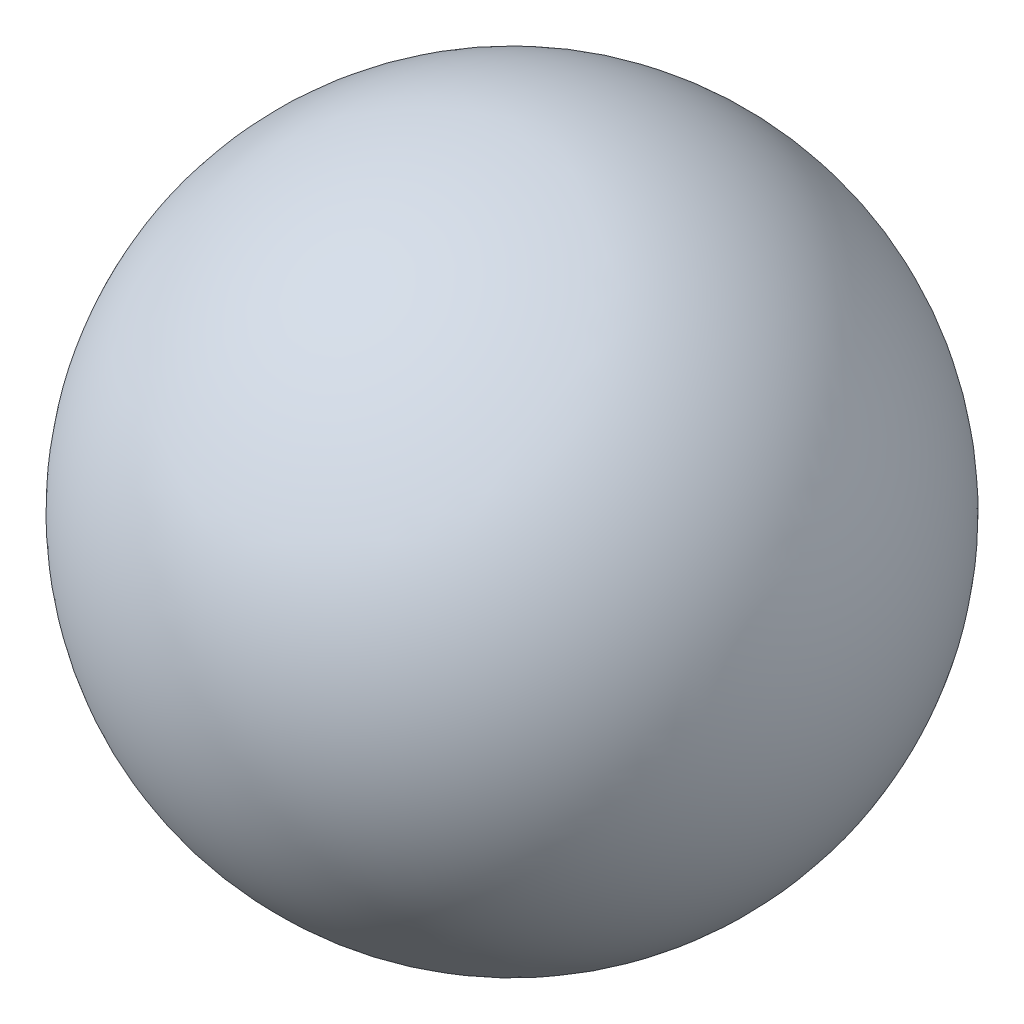
SolidWorks part; units mm, degrees
ref_plane "Plan de face" through (0, 0, 0) normal (0, 0, 1) x (1, 0, 0)
ref_plane "Plan de dessus" through (0, 0, 0) normal (0, 1, 0) x (1, 0, 0)
ref_plane "Plan de droite" through (0, 0, 0) normal (1, 0, 0) x (0, 0, -1)
sketch "Esquisse1" plane through (0, 0, 0) normal (0, 1, 0) x (1, 0, 0)
  line L0 (-250, 0) -> (250, 0)
  arc A0 (250, 0) -> (-250, 0) centre (0, 0) ccw
  dimension "D1" = 500
revolve "Révolution1" add sketch "Esquisse1" angle 360 about L0
ref_plane "Plan1" through (0, 0, 380) normal (0, 0, 1) x (1, 0, 0)
sketch "Esquisse2" plane through (0, 0, 380) normal (0, 0, 1) x (1, 0, 0)
  circle A0 centre (0, 0) radius 91.4874
curve "Hélice/Spirale1"
ref_plane "Plan2" through (0, 0, 350) normal (0, 0, 1) x (1, 0, 0)
sketch "Esquisse3" plane through (0, 0, 350) normal (0, 0, 1) x (1, 0, 0)
  spline S0 degree 3 poles (1010.474, 1620.8253) (291.317, -332.6838) (-108.2126, -145.3785) (-90.5411, 17.9971) (-89.7214, 22.4688) (-87.4254, 31.2681) (-85.9491, 35.5958) (-82.3643, 44.0105) (-80.2559, 48.0976) (-75.446, 55.9391) (-72.7445, 59.6934) (-66.8008, 66.7831) (-63.5586, 70.1186) (-56.5982, 76.2929) (-52.8801, 79.1317) (-45.044, 84.2449) (-40.9261, 86.5193) (-32.3759, 90.4475) (-27.9438, 92.1013) (-18.8588, 94.7452) (-14.206, 95.7352) (-4.779, 97.0226) (-0.0049, 97.3199) (9.5614, 97.2076) (14.3537, 96.7979) (23.8516, 95.2729) (28.5572, 94.1574) (37.7781, 91.2375) (42.2933, 89.433) (51.0323, 85.1669) (55.2561, 82.7053) (63.3169, 77.1718) (67.1537, 74.0999) (74.3525, 67.4063) (77.7143, 63.7847) (83.8843, 56.065) (86.6924, 51.967) (91.6877, 43.3792) (93.8748, 38.8894) (97.5737, 29.612) (99.0854, 24.8245) (101.3932, 15.0532) (102.1893, 10.0695) (103.041, 0.0128) (103.0965, -5.0601) (102.4582, -15.1853) (101.7643, -20.2374) (99.6345, -30.2103) (98.1985, -35.131) (94.6082, -44.7321) (92.4539, -49.4124) (87.4667, -58.4279) (84.6338, -62.763) (78.3443, -70.9897) (74.8878, -74.8813) (67.4203, -82.1315) (63.4094, -85.4901) (54.9152, -91.5953) (50.432, -94.342) (41.0863, -99.1572) (36.224, -101.2258) (26.2226, -104.633) (21.0836, -105.9715) (10.6385, -107.882) (5.3325, -108.4539) (-5.3325, -108.8111) (-10.6913, -108.5963) (-21.3453, -107.3771) (-26.6404, -106.3726) (-37.0505, -103.588) (-42.1654, -101.8079) (-52.1018, -97.5034) (-56.9232, -94.9791) (-66.1641, -89.2341) (-70.5837, -86.0134) (-78.9207, -78.9393) (-82.838, -75.0859) (-90.0801, -66.8244) (-93.4048, -62.4163) (-99.3834, -53.1365) (-102.0372, -48.2648) (-106.6095, -38.1595) (-108.528, -32.9261) (-111.5809, -22.2083) (-112.7153, -16.724) (-114.1676, -5.622) (-114.4856, -0.0042) (-114.2907, 11.2433) (-113.7778, 16.8731) (-111.9243, 28.0219) (-110.5838, 33.5408) (-107.0968, 44.3465) (-104.9504, 49.6332) (-99.8908, 59.8567) (-96.9777, 64.7935) (-90.4415, 74.2061) (-86.8184, 78.682) (-78.9346, 87.071) (-74.674, 90.984) (-65.6023, 98.1567) (-60.7914, 101.4163) (-50.7191, 107.205) (-45.4578, 109.7341) (-34.5956, 114.0001) (-28.9948, 115.7368) (-17.5726, 118.373) (-11.7514, 119.2724) (-0.0135, 120.2067) (5.9031, 120.2416) (17.7033, 119.4382) (23.5869, 118.6001) (35.1926, 116.0612) (40.9146, 114.3605) (52.0708, 110.1261) (57.5049, 107.5924) (67.9641, 101.7399) (72.9891, 98.421) (82.517, 91.0638) (87.0198, 87.0253) (95.4004, 78.3107) (99.2781, 73.6345) (106.3185, 63.7407) (109.4811, 58.5232) (115.016, 47.656) (117.3883, 42.0063) (121.2841, 30.3942) (122.8075, 24.4318) (124.965, 12.3217) (125.599, 6.1741) (125.9562, -6.1741) (125.6793, -12.3745) (124.2131, -24.6935) (123.0237, -30.8119) (119.7505, -42.8328) (117.6667, -48.7351) (112.6426, -60.1931) (109.7023, -65.7487) (103.0221, -76.3892) (99.2822, -81.474) (91.0777, -91.0582) (86.6132, -95.5574) (77.0505, -103.8674) (71.9525, -107.678) (61.2289, -114.5219) (55.6034, -117.5551) (43.9431, -122.7716) (37.9084, -124.9548) (25.5578, -128.4167) (19.2421, -129.6953) (6.4649, -131.3127) (0.0036, -131.6514) (-12.9252, -131.3738) (-19.3925, -130.7576) (-32.1921, -128.5758) (-38.5244, -127.0102) (-50.915, -122.9562) (-56.9731, -120.4677) (-68.6811, -114.6147) (-74.3308, -111.2501) (-85.0954, -103.7112) (-90.2103, -99.5369) (-99.7895, -90.4629) (-104.2537, -85.5632) (-112.4291, -75.1396) (-116.1402, -69.6157) (-122.7224, -58.059) (-125.5935, -52.0262) (-130.4264, -39.5792) (-132.3883, -33.165) (-135.3529, -20.092) (-136.3556, -13.4332) (-137.3724, -0.0142) (-137.3866, 6.746) (-136.4183, 20.2214) (-135.4358, 26.9365) (-132.488, 40.1749) (-130.5226, 46.6982) (-125.6441, 59.4095) (-122.7309, 65.5973) (-116.013, 77.5003) (-112.2083, 83.2153) (-103.7832, 94.0443) (-99.1629, 99.1583) (-89.201, 108.6692) (-83.8596, 113.0661) (-72.5663, 121.0417) (-66.6145, 124.6202) (-54.2256, 130.8748) (-47.7886, 133.5509) (-34.5658, 137.9352) (-27.78, 139.6435) (-14.005, 142.048) (-7.0157, 142.7441) (7.0157, 143.1013) (14.0577, 142.7623) (28.0417, 141.0491) (34.9835, 139.6748) (48.6151, 135.913) (55.3047, 133.5255) (68.2843, 127.7817) (74.5742, 124.4255) (86.6143, 116.8101) (92.3644, 112.5511) (103.1957, 103.2162) (108.2768, 98.1405) (117.6546, 87.2767) (121.9511, 81.4887) (129.6604, 69.3214) (133.073, 62.9421) (138.9336, 49.7267) (141.3816, 42.8907) (145.2524, 28.9074) (146.6753, 21.7602) (148.4577, 7.3079) (148.8171, 0.0029) (148.457, -14.607) (147.7374, -21.9119) (145.2272, -36.3624) (143.4366, -43.508) (138.8155, -57.4834) (135.985, -64.313) (129.3386, -77.5054) (125.5225, -83.8681) (116.9809, -95.9847) (112.2554, -101.7386) (101.9912, -112.508) (96.4525, -117.5234) (84.677, -126.7015) (78.4401, -130.864) (65.3989, -138.2397) (58.5946, -141.4528) (44.5628, -146.8528) (37.3353, -149.0397) (22.6114, -152.3327) (15.1151, -153.4387) (0.0148, -154.5381) (-7.589, -154.5316) (-22.7395, -153.3983) (-30.286, -152.2716) (-45.1572, -148.9148) (-52.4818, -146.6847) (-66.7482, -141.162) (-73.6898, -137.8694) (-87.0365, -130.2862) (-93.4414, -125.9955) (-105.5716, -116.5026) (-111.2968, -111.3004) (-121.9381, -100.0914) (-126.8542, -94.0846) (-135.7648, -81.3918) (-139.7594, -74.7058) (-146.7336, -60.7953) (-149.7134, -53.5709) (-154.5863, -38.7374) (-156.4796, -31.1282) (-159.131, -15.6882) (-159.8892, -7.8573) (-160.2463, 7.8573) (-159.8453, 15.7409) (-157.8851, 31.3899) (-156.3259, 39.1551) (-152.0755, 54.3974) (-149.3843, 61.8744) (-142.9208, 76.3756) (-139.1487, 83.3997) (-130.5982, 96.8393) (-125.8199, 103.2547) (-115.3547, 115.3332) (-109.6678, 120.9963) (-97.5028, 131.4418) (-91.0249, 136.2243) (-77.4139, 144.7989) (-70.2808, 148.5909) (-55.5103, 155.0957) (-47.873, 157.8083) (-32.2569, 162.0882) (-24.2782, 163.6553) (-8.1508, 165.6027) (-0.0022, 165.9828) (16.2889, 165.5401) (24.4313, 164.7172) (40.5327, 161.8787) (48.4916, 159.8629) (64.0518, 154.6748) (71.6529, 151.5024) (86.3298, 144.0624) (93.4054, 139.795) (106.874, 130.2507) (113.2669, 124.9739) (125.2265, 113.5195) (130.7931, 107.3418) (140.9739, 94.2143) (145.5879, 87.2645) (153.7571, 72.7388) (157.3121, 65.163) (163.2792, 49.5464) (165.6912, 41.5056) (169.3125, 25.1308) (170.5218, 16.797) (171.7039, 0.0155) (171.6766, -8.4319) (170.3783, -25.2575) (169.1073, -33.6355) (165.3415, -50.1395) (162.8467, -58.2654) (156.6799, -74.0868) (153.0079, -81.7822) (144.5593, -96.5727) (139.7827, -103.6676) (129.222, -117.0989) (123.4379, -123.4352) (110.9817, -135.2069) (104.3097, -140.6422) (90.2173, -150.488) (82.7971, -154.8985) (67.365, -162.5924) (59.3533, -165.8759) (42.9089, -171.2375) (34.4764, -173.3156) (17.3714, -176.214) (8.6989, -177.0342) (-8.6989, -177.3914) (-17.4242, -176.9283) (-34.7381, -174.7212) (-43.3267, -172.9771) (-60.1797, -168.238) (-68.4441, -165.2431) (-84.4669, -158.06) (-92.2253, -153.8718) (-107.0644, -144.3862) (-114.1451, -139.0888) (-127.4708, -127.4932) (-133.7157, -121.195) (-145.2291, -107.729) (-150.4974, -100.5611) (-159.9374, -85.5063) (-164.1088, -77.6195) (-171.2577, -61.2939) (-174.2351, -52.8553) (-178.9239, -35.6064) (-180.6354, -26.7963) (-182.7477, -8.9938) (-183.1485, -0.0015) (-182.6232, 17.9708) (-181.6971, 26.9507) (-178.5301, 44.703) (-176.2893, 53.4752) (-170.5341, 70.6202) (-167.0197, 78.9928) (-158.7863, 95.1542) (-154.0674, 102.9428) (-143.5204, 117.7633) (-137.6924, 124.7952) (-125.0478, 137.945) (-118.2311, 144.0628) (-103.7516, 155.2463) (-96.0888, 160.3118) (-80.0787, 169.2744) (-71.7314, 173.1714) (-54.53, 179.7056) (-45.6759, 182.3426) (-27.6502, 186.2924) (-18.4788, 187.605) (-0.0162, 188.8696) (9.2749, 188.8216) (27.7756, 187.3584) (36.9851, 185.9431) (55.1218, 181.7683) (64.049, 179.0088) (81.4255, 172.1978) (89.8747, 168.1464) (106.1089, 158.8325) (113.8937, 153.57) (128.6262, 141.9414) (135.5737, 135.5754) (148.4758, 121.8721) (154.4303, 114.5348) (165.2112, 99.0428) (170.0376, 90.8883) (178.4512, 73.9346) (182.0384, 65.1356) (187.8886, 47.0805) (190.1516, 37.8247) (193.297, 19.0546) (194.1793, 9.5405) (194.5365, -9.5405) (194.0113, -19.1074) (191.5572, -38.0863) (189.6282, -47.4983) (184.4005, -65.9621) (181.1019, -75.0137) (173.1991, -92.5582) (168.595, -101.0508) (158.1743, -117.2895) (152.3577, -125.0354) (139.6317, -139.6083) (132.7223, -146.4351) (117.9551, -159.0163) (110.0973, -164.7706) (93.5988, -175.0759) (84.9582, -179.6268) (67.0775, -187.4198) (57.8376, -190.6619) (38.956, -195.7597) (29.3144, -197.6154) (9.8368, -199.8927) (0.0009, -200.3143) (-19.6526, -199.7064) (-29.4701, -198.6769) (-48.8732, -195.1816) (-58.4588, -192.7157) (-77.1886, -186.3934) (-86.3327, -182.5371) (-103.9785, -173.5102) (-112.4801, -168.3398) (-128.6526, -156.7901) (-136.3235, -150.4109) (-150.6635, -136.5761) (-157.3325, -129.1204) (-169.5187, -113.2889) (-175.0357, -104.9132) (-184.7917, -87.4186) (-189.0307, -78.2999) (-196.1319, -59.5136) (-198.9941, -49.8461) (-203.2722, -30.1696) (-204.6881, -20.1607) (-206.0353, -0.0169) (-205.9666, 10.1179) (-204.3384, 30.2937) (-202.7789, 40.3346) (-198.1951, 60.1041) (-195.1708, 69.8326) (-187.7157, 88.7642) (-183.2849, 97.9672) (-173.1056, 115.6451) (-167.3572, 124.1199) (-154.6608, 140.1535) (-147.7129, 147.7122) (-132.7624, 161.7447) (-124.7598, 168.2183) (-107.8684, 179.9344) (-98.9796, 185.1768) (-80.5043, 194.31) (-70.9179, 198.2009) (-51.2521, 204.5397) (-41.1729, 206.9876) (-20.7378, 210.38) (-10.3821, 211.3244) (10.3821, 211.6816) (20.7906, 211.0943) (41.4345, 208.3932) (51.6699, 206.2793) (71.7444, 200.563) (81.5834, 196.9607) (100.6494, 188.3382) (109.8763, 183.3182) (127.5145, 171.9623) (135.9257, 165.6265) (151.7458, 151.7701) (159.1545, 144.2496) (172.8035, 128.1813) (179.0437, 119.6335) (190.2144, 101.6913) (195.1447, 92.2968) (203.5819, 72.8611) (207.0886, 62.8199) (212.5955, 42.3055) (214.5954, 31.8324) (217.0377, 10.6797) (217.48, 0.0002) (216.7895, -21.3345) (215.6567, -31.9895) (211.833, -53.0435) (209.1421, -63.4424) (202.2527, -83.757) (198.0544, -93.6726) (188.2341, -112.8029) (182.6122, -122.0174) (170.0598, -139.5419) (163.1294, -147.8518) (148.1044, -163.382) (140.0097, -170.6022) (122.8263, -183.7911) (113.7376, -189.7595) (94.7585, -200.3091) (84.8683, -204.8901) (64.4972, -212.5583) (54.0164, -215.6456) (32.689, -220.252) (21.8425, -221.7712) (0.0175, -223.201) (-10.9608, -223.1116) (-32.8117, -221.3184) (-43.6841, -219.6146) (-65.0864, -214.6218) (-75.6162, -211.3329) (-96.1029, -203.2336) (-106.0596, -198.4234) (-125.1813, -187.3788) (-134.346, -181.1444) (-151.6808, -167.3802) (-159.8507, -159.8505) (-175.0135, -143.6527) (-182.0063, -134.9849) (-194.6576, -116.6939) (-200.3159, -107.0709) (-210.1688, -87.074) (-214.3634, -76.7002) (-221.1908, -55.4237) (-223.8236, -44.5211) (-271.8364, 247.0391) (205.9965, 622.4196) (1448.7571, -882.426) knots -0.13418 -0.13418 -0.13418 -0.13418 0.003906 0.003906 0.007813 0.007813 0.011719 0.011719 0.015625 0.015625 0.019531 0.019531 0.023438 0.023438 0.027344 0.027344 0.03125 0.03125 0.035156 0.035156 0.039062 0.039062 0.042969 0.042969 0.046875 0.046875 0.050781 0.050781 0.054687 0.054687 0.058594 0.058594 0.0625 0.0625 0.066406 0.066406 0.070312 0.070312 0.074219 0.074219 0.078125 0.078125 0.082031 0.082031 0.085937 0.085937 0.089844 0.089844 0.09375 0.09375 0.097656 0.097656 0.101562 0.101562 0.105469 0.105469 0.109375 0.109375 0.113281 0.113281 0.117187 0.117187 0.121094 0.121094 0.125 0.125 0.128906 0.128906 0.132812 0.132812 0.136719 0.136719 0.140625 0.140625 0.144531 0.144531 0.148437 0.148437 0.152344 0.152344 0.15625 0.15625 0.160156 0.160156 0.164062 0.164062 0.167969 0.167969 0.171875 0.171875 0.175781 0.175781 0.179687 0.179687 0.183594 0.183594 0.1875 0.1875 0.191406 0.191406 0.195312 0.195312 0.199219 0.199219 0.203125 0.203125 0.207031 0.207031 0.210937 0.210937 0.214844 0.214844 0.21875 0.21875 0.222656 0.222656 0.226562 0.226562 0.230469 0.230469 0.234375 0.234375 0.238281 0.238281 0.242187 0.242187 0.246094 0.246094 0.25 0.25 0.253906 0.253906 0.257812 0.257812 0.261719 0.261719 0.265625 0.265625 0.269531 0.269531 0.273437 0.273437 0.277344 0.277344 0.28125 0.28125 0.285156 0.285156 0.289062 0.289062 0.292969 0.292969 0.296875 0.296875 0.300781 0.300781 0.304687 0.304687 0.308594 0.308594 0.3125 0.3125 0.316406 0.316406 0.320312 0.320312 0.324219 0.324219 0.328125 0.328125 0.332031 0.332031 0.335937 0.335937 0.339844 0.339844 0.34375 0.34375 0.347656 0.347656 0.351562 0.351562 0.355469 0.355469 0.359375 0.359375 0.363281 0.363281 0.367187 0.367187 0.371094 0.371094 0.375 0.375 0.378906 0.378906 0.382812 0.382812 0.386719 0.386719 0.390625 0.390625 0.394531 0.394531 0.398437 0.398437 0.402344 0.402344 0.40625 0.40625 0.410156 0.410156 0.414062 0.414062 0.417969 0.417969 0.421875 0.421875 0.425781 0.425781 0.429687 0.429687 0.433594 0.433594 0.4375 0.4375 0.441406 0.441406 0.445312 0.445312 0.449219 0.449219 0.453125 0.453125 0.457031 0.457031 0.460937 0.460937 0.464844 0.464844 0.46875 0.46875 0.472656 0.472656 0.476562 0.476562 0.480469 0.480469 0.484375 0.484375 0.488281 0.488281 0.492187 0.492187 0.496094 0.496094 0.5 0.5 0.503906 0.503906 0.507812 0.507812 0.511719 0.511719 0.515625 0.515625 0.519531 0.519531 0.523437 0.523437 0.527344 0.527344 0.53125 0.53125 0.535156 0.535156 0.539062 0.539062 0.542969 0.542969 0.546875 0.546875 0.550781 0.550781 0.554687 0.554687 0.558594 0.558594 0.5625 0.5625 0.566406 0.566406 0.570312 0.570312 0.574219 0.574219 0.578125 0.578125 0.582031 0.582031 0.585937 0.585937 0.589844 0.589844 0.59375 0.59375 0.597656 0.597656 0.601562 0.601562 0.605469 0.605469 0.609375 0.609375 0.613281 0.613281 0.617187 0.617187 0.621094 0.621094 0.625 0.625 0.628906 0.628906 0.632812 0.632812 0.636719 0.636719 0.640625 0.640625 0.644531 0.644531 0.648437 0.648437 0.652344 0.652344 0.65625 0.65625 0.660156 0.660156 0.664062 0.664062 0.667969 0.667969 0.671875 0.671875 0.675781 0.675781 0.679687 0.679687 0.683594 0.683594 0.6875 0.6875 0.691406 0.691406 0.695312 0.695312 0.699219 0.699219 0.703125 0.703125 0.707031 0.707031 0.710937 0.710937 0.714844 0.714844 0.71875 0.71875 0.722656 0.722656 0.726562 0.726562 0.730469 0.730469 0.734375 0.734375 0.738281 0.738281 0.742187 0.742187 0.746094 0.746094 0.75 0.75 0.753906 0.753906 0.757812 0.757812 0.761719 0.761719 0.765625 0.765625 0.769531 0.769531 0.773438 0.773438 0.777344 0.777344 0.78125 0.78125 0.785156 0.785156 0.789062 0.789062 0.792969 0.792969 0.796875 0.796875 0.800781 0.800781 0.804688 0.804688 0.808594 0.808594 0.8125 0.8125 0.816406 0.816406 0.820312 0.820312 0.824219 0.824219 0.828125 0.828125 0.832031 0.832031 0.835938 0.835938 0.839844 0.839844 0.84375 0.84375 0.847656 0.847656 0.851562 0.851562 0.855469 0.855469 0.859375 0.859375 0.863281 0.863281 0.867188 0.867188 0.871094 0.871094 0.875 0.875 0.878906 0.878906 0.882812 0.882812 0.886719 0.886719 0.890625 0.890625 0.894531 0.894531 0.898438 0.898438 0.902344 0.902344 0.90625 0.90625 0.910156 0.910156 0.914062 0.914062 0.917969 0.917969 0.921875 0.921875 0.925781 0.925781 0.929688 0.929688 0.933594 0.933594 0.9375 0.9375 0.941406 0.941406 0.945312 0.945312 0.949219 0.949219 0.953125 0.953125 0.957031 0.957031 0.960938 0.960938 0.964844 0.964844 0.96875 0.96875 0.972656 0.972656 0.976562 0.976562 0.980469 0.980469 0.984375 0.984375 0.988281 0.988281 0.992188 0.992188 0.996094 0.996094 1.095256 1.095256 1.095256 1.095256 only from (-91.4874, 0) to (-228.6481, 0) construction
  spline S1 degree 3 poles (-91.4874, 0) (-91.666, 4.4909) (-91.5133, 9.0081) (-90.5411, 17.9971) (-89.7214, 22.4688) (-87.4254, 31.2681) (-85.9491, 35.5958) (-82.3643, 44.0105) (-80.2559, 48.0976) (-75.446, 55.9391) (-72.7445, 59.6934) (-66.8008, 66.7831) (-63.5586, 70.1186) (-56.5982, 76.2929) (-52.8801, 79.1317) (-45.044, 84.2449) (-40.9261, 86.5193) (-32.3759, 90.4475) (-27.9438, 92.1013) (-18.8588, 94.7452) (-14.206, 95.7352) (-4.779, 97.0226) (-0.0049, 97.3199) (9.5614, 97.2076) (14.3537, 96.7979) (23.8516, 95.2729) (28.5572, 94.1574) (37.7781, 91.2375) (42.2933, 89.433) (51.0323, 85.1669) (55.2561, 82.7053) (63.3169, 77.1718) (67.1537, 74.0999) (74.3525, 67.4063) (77.7143, 63.7847) (83.8843, 56.065) (86.6924, 51.967) (91.6877, 43.3792) (93.8748, 38.8894) (97.5737, 29.612) (99.0854, 24.8245) (101.3932, 15.0532) (102.1893, 10.0695) (103.041, 0.0128) (103.0965, -5.0601) (102.4582, -15.1853) (101.7643, -20.2374) (99.6345, -30.2103) (98.1985, -35.131) (94.6082, -44.7321) (92.4539, -49.4124) (87.4667, -58.4279) (84.6338, -62.763) (78.3443, -70.9897) (74.8878, -74.8813) (67.4203, -82.1315) (63.4094, -85.4901) (54.9152, -91.5953) (50.432, -94.342) (41.0863, -99.1572) (36.224, -101.2258) (26.2226, -104.633) (21.0836, -105.9715) (10.6385, -107.882) (5.3325, -108.4539) (-5.3325, -108.8111) (-10.6913, -108.5963) (-21.3453, -107.3771) (-26.6404, -106.3726) (-37.0505, -103.588) (-42.1654, -101.8079) (-52.1018, -97.5034) (-56.9232, -94.9791) (-66.1641, -89.2341) (-70.5837, -86.0134) (-78.9207, -78.9393) (-82.838, -75.0859) (-90.0801, -66.8244) (-93.4048, -62.4163) (-99.3834, -53.1365) (-102.0372, -48.2648) (-106.6095, -38.1595) (-108.528, -32.9261) (-111.5809, -22.2083) (-112.7153, -16.724) (-114.1676, -5.622) (-114.4856, -0.0042) (-114.2907, 11.2433) (-113.7778, 16.8731) (-111.9243, 28.0219) (-110.5838, 33.5408) (-107.0968, 44.3465) (-104.9504, 49.6332) (-99.8908, 59.8567) (-96.9777, 64.7935) (-90.4415, 74.2061) (-86.8184, 78.682) (-78.9346, 87.071) (-74.674, 90.984) (-65.6023, 98.1567) (-60.7914, 101.4163) (-50.7191, 107.205) (-45.4578, 109.7341) (-34.5956, 114.0001) (-28.9948, 115.7368) (-17.5726, 118.373) (-11.7514, 119.2724) (-0.0135, 120.2067) (5.9031, 120.2416) (17.7033, 119.4382) (23.5869, 118.6001) (35.1926, 116.0612) (40.9146, 114.3605) (52.0708, 110.1261) (57.5049, 107.5924) (67.9641, 101.7399) (72.9891, 98.421) (82.517, 91.0638) (87.0198, 87.0253) (95.4004, 78.3107) (99.2781, 73.6345) (106.3185, 63.7407) (109.4811, 58.5232) (115.016, 47.656) (117.3883, 42.0063) (121.2841, 30.3942) (122.8075, 24.4318) (124.965, 12.3217) (125.599, 6.1741) (125.9562, -6.1741) (125.6793, -12.3745) (124.2131, -24.6935) (123.0237, -30.8119) (119.7505, -42.8328) (117.6667, -48.7351) (112.6426, -60.1931) (109.7023, -65.7487) (103.0221, -76.3892) (99.2822, -81.474) (91.0777, -91.0582) (86.6132, -95.5574) (77.0505, -103.8674) (71.9525, -107.678) (61.2289, -114.5219) (55.6034, -117.5551) (43.9431, -122.7716) (37.9084, -124.9548) (25.5578, -128.4167) (19.2421, -129.6953) (6.4649, -131.3127) (0.0036, -131.6514) (-12.9252, -131.3738) (-19.3925, -130.7576) (-32.1921, -128.5758) (-38.5244, -127.0102) (-50.915, -122.9562) (-56.9731, -120.4677) (-68.6811, -114.6147) (-74.3308, -111.2501) (-85.0954, -103.7112) (-90.2103, -99.5369) (-99.7895, -90.4629) (-104.2537, -85.5632) (-112.4291, -75.1396) (-116.1402, -69.6157) (-122.7224, -58.059) (-125.5935, -52.0262) (-130.4264, -39.5792) (-132.3883, -33.165) (-135.3529, -20.092) (-136.3556, -13.4332) (-137.3724, -0.0142) (-137.3866, 6.746) (-136.4183, 20.2214) (-135.4358, 26.9365) (-132.488, 40.1749) (-130.5226, 46.6982) (-125.6441, 59.4095) (-122.7309, 65.5973) (-116.013, 77.5003) (-112.2083, 83.2153) (-103.7832, 94.0443) (-99.1629, 99.1583) (-89.201, 108.6692) (-83.8596, 113.0661) (-72.5663, 121.0417) (-66.6145, 124.6202) (-54.2256, 130.8748) (-47.7886, 133.5509) (-34.5658, 137.9352) (-27.78, 139.6435) (-14.005, 142.048) (-7.0157, 142.7441) (7.0157, 143.1013) (14.0577, 142.7623) (28.0417, 141.0491) (34.9835, 139.6748) (48.6151, 135.913) (55.3047, 133.5255) (68.2843, 127.7817) (74.5742, 124.4255) (86.6143, 116.8101) (92.3644, 112.5511) (103.1957, 103.2162) (108.2768, 98.1405) (117.6546, 87.2767) (121.9511, 81.4887) (129.6604, 69.3214) (133.073, 62.9421) (138.9336, 49.7267) (141.3816, 42.8907) (145.2524, 28.9074) (146.6753, 21.7602) (148.4577, 7.3079) (148.8171, 0.0029) (148.457, -14.607) (147.7374, -21.9119) (145.2272, -36.3624) (143.4366, -43.508) (138.8155, -57.4834) (135.985, -64.313) (129.3386, -77.5054) (125.5225, -83.8681) (116.9809, -95.9847) (112.2554, -101.7386) (101.9912, -112.508) (96.4525, -117.5234) (84.677, -126.7015) (78.4401, -130.864) (65.3989, -138.2397) (58.5946, -141.4528) (44.5628, -146.8528) (37.3353, -149.0397) (22.6114, -152.3327) (15.1151, -153.4387) (0.0148, -154.5381) (-7.589, -154.5316) (-22.7395, -153.3983) (-30.286, -152.2716) (-45.1572, -148.9148) (-52.4818, -146.6847) (-66.7482, -141.162) (-73.6898, -137.8694) (-87.0365, -130.2862) (-93.4414, -125.9955) (-105.5716, -116.5026) (-111.2968, -111.3004) (-121.9381, -100.0914) (-126.8542, -94.0846) (-135.7648, -81.3918) (-139.7594, -74.7058) (-146.7336, -60.7953) (-149.7134, -53.5709) (-154.5863, -38.7374) (-156.4796, -31.1282) (-159.131, -15.6882) (-159.8892, -7.8573) (-160.2463, 7.8573) (-159.8453, 15.7409) (-157.8851, 31.3899) (-156.3259, 39.1551) (-152.0755, 54.3974) (-149.3843, 61.8744) (-142.9208, 76.3756) (-139.1487, 83.3997) (-130.5982, 96.8393) (-125.8199, 103.2547) (-115.3547, 115.3332) (-109.6678, 120.9963) (-97.5028, 131.4418) (-91.0249, 136.2243) (-77.4139, 144.7989) (-70.2808, 148.5909) (-55.5103, 155.0957) (-47.873, 157.8083) (-32.2569, 162.0882) (-24.2782, 163.6553) (-8.1508, 165.6027) (-0.0022, 165.9828) (16.2889, 165.5401) (24.4313, 164.7172) (40.5327, 161.8787) (48.4916, 159.8629) (64.0518, 154.6748) (71.6529, 151.5024) (86.3298, 144.0624) (93.4054, 139.795) (106.874, 130.2507) (113.2669, 124.9739) (125.2265, 113.5195) (130.7931, 107.3418) (140.9739, 94.2143) (145.5879, 87.2645) (153.7571, 72.7388) (157.3121, 65.163) (163.2792, 49.5464) (165.6912, 41.5056) (169.3125, 25.1308) (170.5218, 16.797) (171.7039, 0.0155) (171.6766, -8.4319) (170.3783, -25.2575) (169.1073, -33.6355) (165.3415, -50.1395) (162.8467, -58.2654) (156.6799, -74.0868) (153.0079, -81.7822) (144.5593, -96.5727) (139.7827, -103.6676) (129.222, -117.0989) (123.4379, -123.4352) (110.9817, -135.2069) (104.3097, -140.6422) (90.2173, -150.488) (82.7971, -154.8985) (67.365, -162.5924) (59.3533, -165.8759) (42.9089, -171.2375) (34.4764, -173.3156) (17.3714, -176.214) (8.6989, -177.0342) (-8.6989, -177.3914) (-17.4242, -176.9283) (-34.7381, -174.7212) (-43.3267, -172.9771) (-60.1797, -168.238) (-68.4441, -165.2431) (-84.4669, -158.06) (-92.2253, -153.8718) (-107.0644, -144.3862) (-114.1451, -139.0888) (-127.4708, -127.4932) (-133.7157, -121.195) (-145.2291, -107.729) (-150.4974, -100.5611) (-159.9374, -85.5063) (-164.1088, -77.6195) (-171.2577, -61.2939) (-174.2351, -52.8553) (-178.9239, -35.6064) (-180.6354, -26.7963) (-182.7477, -8.9938) (-183.1485, -0.0015) (-182.6232, 17.9708) (-181.6971, 26.9507) (-178.5301, 44.703) (-176.2893, 53.4752) (-170.5341, 70.6202) (-167.0197, 78.9928) (-158.7863, 95.1542) (-154.0674, 102.9428) (-143.5204, 117.7633) (-137.6924, 124.7952) (-125.0478, 137.945) (-118.2311, 144.0628) (-103.7516, 155.2463) (-96.0888, 160.3118) (-80.0787, 169.2744) (-71.7314, 173.1714) (-54.53, 179.7056) (-45.6759, 182.3426) (-27.6502, 186.2924) (-18.4788, 187.605) (-0.0162, 188.8696) (9.2749, 188.8216) (27.7756, 187.3584) (36.9851, 185.9431) (55.1218, 181.7683) (64.049, 179.0088) (81.4255, 172.1978) (89.8747, 168.1464) (106.1089, 158.8325) (113.8937, 153.57) (128.6262, 141.9414) (135.5737, 135.5754) (148.4758, 121.8721) (154.4303, 114.5348) (165.2112, 99.0428) (170.0376, 90.8883) (178.4512, 73.9346) (182.0384, 65.1356) (187.8886, 47.0805) (190.1516, 37.8247) (193.297, 19.0546) (194.1793, 9.5405) (194.5365, -9.5405) (194.0113, -19.1074) (191.5572, -38.0863) (189.6282, -47.4983) (184.4005, -65.9621) (181.1019, -75.0137) (173.1991, -92.5582) (168.595, -101.0508) (158.1743, -117.2895) (152.3577, -125.0354) (139.6317, -139.6083) (132.7223, -146.4351) (117.9551, -159.0163) (110.0973, -164.7706) (93.5988, -175.0759) (84.9582, -179.6268) (67.0775, -187.4198) (57.8376, -190.6619) (38.956, -195.7597) (29.3144, -197.6154) (9.8368, -199.8927) (0.0009, -200.3143) (-19.6526, -199.7064) (-29.4701, -198.6769) (-48.8732, -195.1816) (-58.4588, -192.7157) (-77.1886, -186.3934) (-86.3327, -182.5371) (-103.9785, -173.5102) (-112.4801, -168.3398) (-128.6526, -156.7901) (-136.3235, -150.4109) (-150.6635, -136.5761) (-157.3325, -129.1204) (-169.5187, -113.2889) (-175.0357, -104.9132) (-184.7917, -87.4186) (-189.0307, -78.2999) (-196.1319, -59.5136) (-198.9941, -49.8461) (-203.2722, -30.1696) (-204.6881, -20.1607) (-206.0353, -0.0169) (-205.9666, 10.1179) (-204.3384, 30.2937) (-202.7789, 40.3346) (-198.1951, 60.1041) (-195.1708, 69.8326) (-187.7157, 88.7642) (-183.2849, 97.9672) (-173.1056, 115.6451) (-167.3572, 124.1199) (-154.6608, 140.1535) (-147.7129, 147.7122) (-132.7624, 161.7447) (-124.7598, 168.2183) (-107.8684, 179.9344) (-98.9796, 185.1768) (-80.5043, 194.31) (-70.9179, 198.2009) (-51.2521, 204.5397) (-41.1729, 206.9876) (-20.7378, 210.38) (-10.3821, 211.3244) (10.3821, 211.6816) (20.7906, 211.0943) (41.4345, 208.3932) (51.6699, 206.2793) (71.7444, 200.563) (81.5834, 196.9607) (100.6494, 188.3382) (109.8763, 183.3182) (127.5145, 171.9623) (135.9257, 165.6265) (151.7458, 151.7701) (159.1545, 144.2496) (172.8035, 128.1813) (179.0437, 119.6335) (190.2144, 101.6913) (195.1447, 92.2968) (203.5819, 72.8611) (207.0886, 62.8199) (212.5955, 42.3055) (214.5954, 31.8324) (217.0377, 10.6797) (217.48, 0.0002) (216.7895, -21.3345) (215.6567, -31.9895) (211.833, -53.0435) (209.1421, -63.4424) (202.2527, -83.757) (198.0544, -93.6726) (188.2341, -112.8029) (182.6122, -122.0174) (170.0598, -139.5419) (163.1294, -147.8518) (148.1044, -163.382) (140.0097, -170.6022) (122.8263, -183.7911) (113.7376, -189.7595) (94.7585, -200.3091) (84.8683, -204.8901) (64.4972, -212.5583) (54.0164, -215.6456) (32.689, -220.252) (21.8425, -221.7712) (0.0175, -223.201) (-10.9608, -223.1116) (-32.8117, -221.3184) (-43.6841, -219.6146) (-65.0864, -214.6218) (-75.6162, -211.3329) (-96.1029, -203.2336) (-106.0596, -198.4234) (-125.1813, -187.3788) (-134.346, -181.1444) (-151.6808, -167.3802) (-159.8507, -159.8505) (-175.0135, -143.6527) (-182.0063, -134.9849) (-194.6576, -116.6939) (-200.3159, -107.0709) (-210.1688, -87.074) (-214.3634, -76.7002) (-221.1908, -55.4237) (-223.8236, -44.5211) (-227.463, -22.421) (-228.4695, -11.2237) (-228.6481, 0) knots 0 0 0 0 0.003906 0.003906 0.007813 0.007813 0.011719 0.011719 0.015625 0.015625 0.019531 0.019531 0.023438 0.023438 0.027344 0.027344 0.03125 0.03125 0.035156 0.035156 0.039062 0.039062 0.042969 0.042969 0.046875 0.046875 0.050781 0.050781 0.054687 0.054687 0.058594 0.058594 0.0625 0.0625 0.066406 0.066406 0.070312 0.070312 0.074219 0.074219 0.078125 0.078125 0.082031 0.082031 0.085937 0.085937 0.089844 0.089844 0.09375 0.09375 0.097656 0.097656 0.101562 0.101562 0.105469 0.105469 0.109375 0.109375 0.113281 0.113281 0.117187 0.117187 0.121094 0.121094 0.125 0.125 0.128906 0.128906 0.132812 0.132812 0.136719 0.136719 0.140625 0.140625 0.144531 0.144531 0.148437 0.148437 0.152344 0.152344 0.15625 0.15625 0.160156 0.160156 0.164062 0.164062 0.167969 0.167969 0.171875 0.171875 0.175781 0.175781 0.179687 0.179687 0.183594 0.183594 0.1875 0.1875 0.191406 0.191406 0.195312 0.195312 0.199219 0.199219 0.203125 0.203125 0.207031 0.207031 0.210937 0.210937 0.214844 0.214844 0.21875 0.21875 0.222656 0.222656 0.226562 0.226562 0.230469 0.230469 0.234375 0.234375 0.238281 0.238281 0.242187 0.242187 0.246094 0.246094 0.25 0.25 0.253906 0.253906 0.257812 0.257812 0.261719 0.261719 0.265625 0.265625 0.269531 0.269531 0.273437 0.273437 0.277344 0.277344 0.28125 0.28125 0.285156 0.285156 0.289062 0.289062 0.292969 0.292969 0.296875 0.296875 0.300781 0.300781 0.304687 0.304687 0.308594 0.308594 0.3125 0.3125 0.316406 0.316406 0.320312 0.320312 0.324219 0.324219 0.328125 0.328125 0.332031 0.332031 0.335937 0.335937 0.339844 0.339844 0.34375 0.34375 0.347656 0.347656 0.351562 0.351562 0.355469 0.355469 0.359375 0.359375 0.363281 0.363281 0.367187 0.367187 0.371094 0.371094 0.375 0.375 0.378906 0.378906 0.382812 0.382812 0.386719 0.386719 0.390625 0.390625 0.394531 0.394531 0.398437 0.398437 0.402344 0.402344 0.40625 0.40625 0.410156 0.410156 0.414062 0.414062 0.417969 0.417969 0.421875 0.421875 0.425781 0.425781 0.429687 0.429687 0.433594 0.433594 0.4375 0.4375 0.441406 0.441406 0.445312 0.445312 0.449219 0.449219 0.453125 0.453125 0.457031 0.457031 0.460937 0.460937 0.464844 0.464844 0.46875 0.46875 0.472656 0.472656 0.476562 0.476562 0.480469 0.480469 0.484375 0.484375 0.488281 0.488281 0.492187 0.492187 0.496094 0.496094 0.5 0.5 0.503906 0.503906 0.507812 0.507812 0.511719 0.511719 0.515625 0.515625 0.519531 0.519531 0.523437 0.523437 0.527344 0.527344 0.53125 0.53125 0.535156 0.535156 0.539062 0.539062 0.542969 0.542969 0.546875 0.546875 0.550781 0.550781 0.554687 0.554687 0.558594 0.558594 0.5625 0.5625 0.566406 0.566406 0.570312 0.570312 0.574219 0.574219 0.578125 0.578125 0.582031 0.582031 0.585937 0.585937 0.589844 0.589844 0.59375 0.59375 0.597656 0.597656 0.601562 0.601562 0.605469 0.605469 0.609375 0.609375 0.613281 0.613281 0.617187 0.617187 0.621094 0.621094 0.625 0.625 0.628906 0.628906 0.632812 0.632812 0.636719 0.636719 0.640625 0.640625 0.644531 0.644531 0.648437 0.648437 0.652344 0.652344 0.65625 0.65625 0.660156 0.660156 0.664062 0.664062 0.667969 0.667969 0.671875 0.671875 0.675781 0.675781 0.679687 0.679687 0.683594 0.683594 0.6875 0.6875 0.691406 0.691406 0.695312 0.695312 0.699219 0.699219 0.703125 0.703125 0.707031 0.707031 0.710937 0.710937 0.714844 0.714844 0.71875 0.71875 0.722656 0.722656 0.726562 0.726562 0.730469 0.730469 0.734375 0.734375 0.738281 0.738281 0.742187 0.742187 0.746094 0.746094 0.75 0.75 0.753906 0.753906 0.757812 0.757812 0.761719 0.761719 0.765625 0.765625 0.769531 0.769531 0.773438 0.773438 0.777344 0.777344 0.78125 0.78125 0.785156 0.785156 0.789062 0.789062 0.792969 0.792969 0.796875 0.796875 0.800781 0.800781 0.804688 0.804688 0.808594 0.808594 0.8125 0.8125 0.816406 0.816406 0.820312 0.820312 0.824219 0.824219 0.828125 0.828125 0.832031 0.832031 0.835938 0.835938 0.839844 0.839844 0.84375 0.84375 0.847656 0.847656 0.851562 0.851562 0.855469 0.855469 0.859375 0.859375 0.863281 0.863281 0.867188 0.867188 0.871094 0.871094 0.875 0.875 0.878906 0.878906 0.882812 0.882812 0.886719 0.886719 0.890625 0.890625 0.894531 0.894531 0.898438 0.898438 0.902344 0.902344 0.90625 0.90625 0.910156 0.910156 0.914062 0.914062 0.917969 0.917969 0.921875 0.921875 0.925781 0.925781 0.929688 0.929688 0.933594 0.933594 0.9375 0.9375 0.941406 0.941406 0.945312 0.945312 0.949219 0.949219 0.953125 0.953125 0.957031 0.957031 0.960938 0.960938 0.964844 0.964844 0.96875 0.96875 0.972656 0.972656 0.976562 0.976562 0.980469 0.980469 0.984375 0.984375 0.988281 0.988281 0.992188 0.992188 0.996094 0.996094 1 1 1 1
curve "Courbe2"
